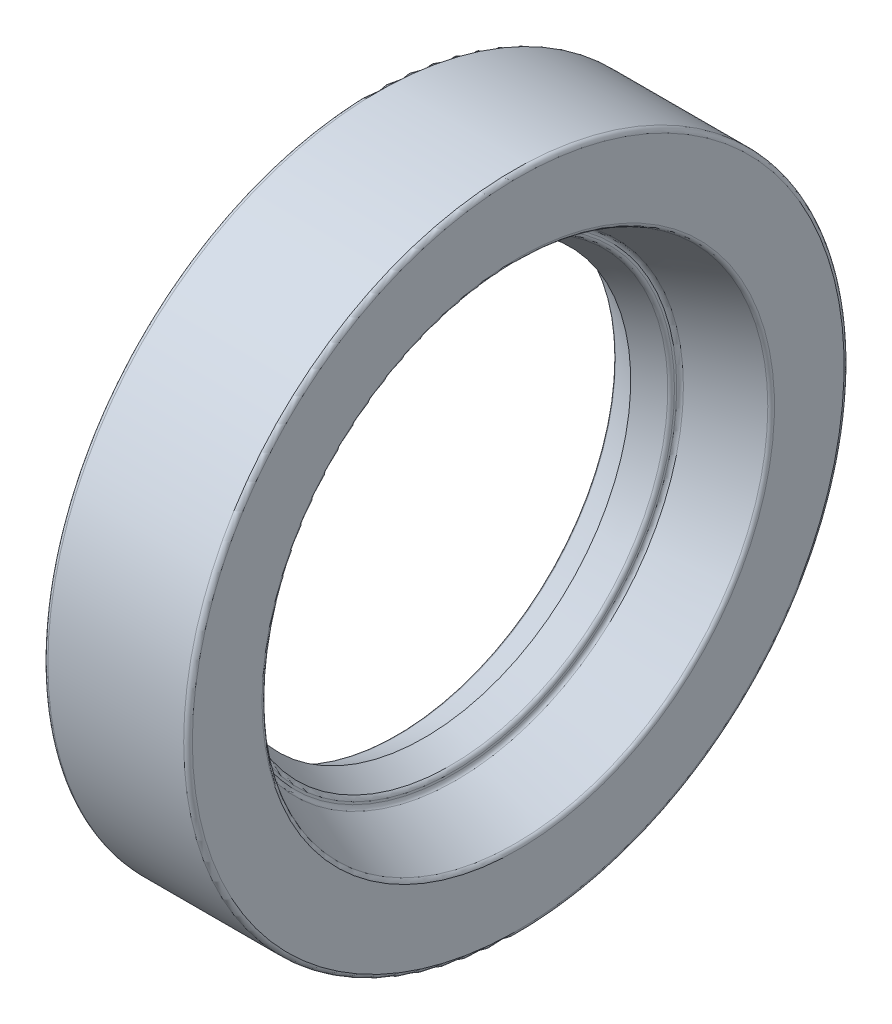
SolidWorks part; units mm, degrees
ref_plane "Přední rovina" through (0, 0, 0) normal (0, 0, 1) x (1, 0, 0)
ref_plane "Vrchní rovina" through (0, 0, 0) normal (0, 1, 0) x (1, 0, 0)
ref_plane "Pravá rovina" through (0, 0, 0) normal (1, 0, 0) x (0, 0, -1)
sketch "Skica1" plane through (0, 0, 0) normal (0, 0, 1) x (1, 0, 0)
  line L0 (0, 0) -> (4.55, 0) construction
  line L1 (-2.45, 16) -> (4.55, 16)
  line L2 (4.55, 16) -> (4.55, 12.275)
  line L3 (4.55, 12.275) -> (1.4, 10.9702)
  line L4 (1.4, 10.9702) -> (1.4, 10.5799)
  line L5 (1.4, 10.5799) -> (0, 10)
  line L6 (0, 10) -> (-1.4, 10.5799)
  line L7 (-1.4, 10.5799) -> (-1.4, 11.75)
  line L8 (-1.4, 11.75) -> (-0.525, 11.75)
  line L9 (0.525, 11.75) -> (1.9655, 11.75)
  line L10 (1.9655, 11.75) -> (3.5, 12.3856)
  line L11 (3.5, 12.3856) -> (3.5, 14.9522)
  line L12 (3.5, 14.9522) -> (-2.45, 15.16)
  line L13 (-2.45, 15.16) -> (-2.45, 16)
  line L14 (0, 11.75) -> (0, 10) construction
  arc A0 (-0.525, 11.75) -> (0.525, 11.75) centre (0, 11.75) ccw
  dimension "D7" = 0.525
  dimension "D1" = 32
  dimension "D2" = 7
  dimension "D3" = 4.55
  dimension "D4" = 20
  dimension "D5" = 0.84
  dimension "D6" = 1.05
  dimension "D8" = 1.75
  dimension "D9" = 0.504
  dimension "D10" = 1.4
  dimension "D11" = 135
  dimension "D12" = 2.275
  dimension "D13" = 2
revolve "Otočit kolem osy1" add sketch "Skica1" angle 360 about L0
fillet "Zaoblit1" radius 0.21 11 edges at (1.4, 0, 10.9702) (1.4, 0, 10.5799) (-1.4, 0, 10.5799) (-1.4, 0, 11.75) (1.9655, 0, 11.75) (3.5, 0, 12.3856) (3.5, 0, 14.9522) (-2.45, 0, 15.16) (-2.45, 0, 16) (4.55, 0, 12.275) (4.55, 0, 16)
sketch "Skica2" plane through (0, 0, 0) normal (0, 1, 0) x (1, 0, 0)
  circle A0 centre (0, 11.75) radius 0.525
  arc A1 (-0.525, 11.75) -> (0.525, 11.75) centre (0, 11.75) ccw construction
  circle A2 centre (0, 11.75) radius 0.105
  circle A3 centre (0, 11.75) radius 0.4255
  dimension "D1" = 0.0995
  dimension "D2" = 0.21
revolve "Otočit kolem osy3" add sketch "Skica2" angle 360 about axis through (0, 0, 0) along (1, 0, 0)
equation "\"D3@Skica1\"=\"D2@Skica1\" * 0.65"
equation "\"D5@Skica1\" = \"D2@Skica1\" * 0.12"
equation "\"D6@Skica1\" = \"D2@Skica1\" * 0.15"
equation "\"D7@Skica1\" = \"D2@Skica1\" * 0.075"
equation "\"D8@Skica1\" = \"D2@Skica1\" * 0.25"
equation "\"D9@Skica1\" = \"D5@Skica1\"*0.6"
equation "\"D10@Skica1\" = \"D8@Skica1\" * 0.8"
equation "\"D12@Skica1\" = \"D8@Skica1\" * 1.3"
equation "\"D1@Zaoblit1\" = \"D2@Skica1\" * 0.03"
equation "\"D2@Skica2\" = \"D7@Skica1\"*0.4"
